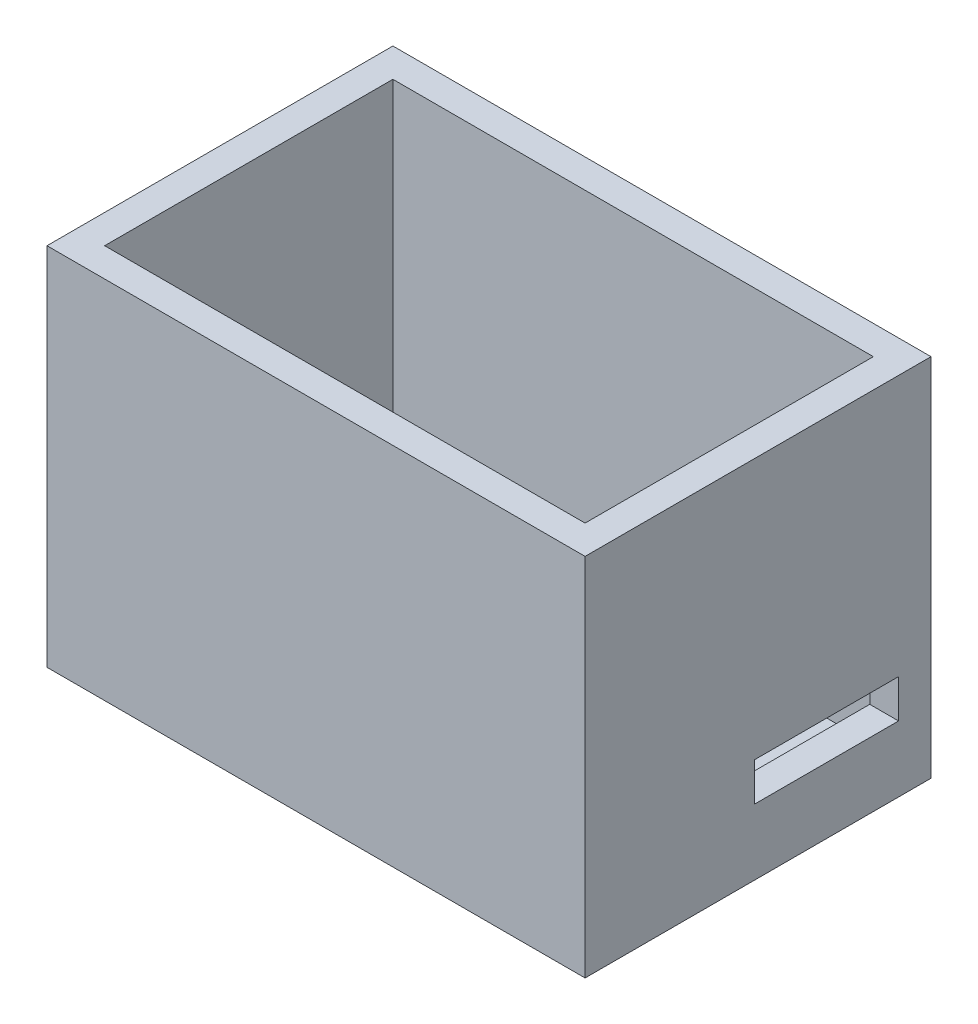
SolidWorks part; units mm, degrees
ref_plane "Plano frontal" through (0, 0, 0) normal (0, 0, 1) x (1, 0, 0)
ref_plane "Plano superior" through (0, 0, 0) normal (0, 1, 0) x (1, 0, 0)
ref_plane "Plano direito" through (0, 0, 0) normal (1, 0, 0) x (0, 0, -1)
sketch "Esboço1" plane through (0, 0, 0) normal (0, 1, 0) x (1, 0, 0)
  line L1 (-60.3352, 26.656) -> (-10.3352, 26.656)
  line L2 (-60.3352, 26.656) -> (-60.3352, -3.344)
  line L3 (-60.3352, -3.344) -> (-10.3352, -3.344)
  line L4 (-10.3352, 26.656) -> (-10.3352, -3.344)
  dimension "D1" = 50
  dimension "D2" = 30
extrude "Ressalto-extrusão1" add sketch "Esboço1" along normal blind 35
shell "Casca1" thickness 3
sketch "Esboço3" plane through (-7.3352, 0, 0) normal (1, 0, 0) x (0, 0, -1)
  line L1 (26.2815, 7.8528) -> (11.2815, 7.8528)
  line L2 (26.2815, 7.8528) -> (26.2815, 3.8528)
  line L3 (26.2815, 3.8528) -> (11.2815, 3.8528)
  line L4 (11.2815, 7.8528) -> (11.2815, 3.8528)
  dimension "D1" = 15
extrude "Corte-extrusão2" cut sketch "Esboço3" against normal blind 35
sketch "Esboço4" plane through (0, 0, 0) normal (0, 1, 0) x (1, 0, 0)
  line L0 (-35.3352, 26.656) -> (-35.3352, -3.344) construction
  line L1 (-10.3352, 26.656) -> (-60.3352, 26.656) construction
  line L2 (-60.3352, -3.344) -> (-10.3352, -3.344) construction
  line L3 (-10.3352, 11.656) -> (-60.3352, 11.656) construction
  line L4 (-10.3352, -3.344) -> (-10.3352, 26.656) construction
  line L5 (-60.3352, 26.656) -> (-60.3352, -3.344) construction
  circle A0 centre (-44.2282, 17.7212) radius 2
  circle A1 centre (-44.2282, 5.5908) radius 2
  circle A2 centre (-26.4422, 5.5908) radius 2
  circle A3 centre (-26.4422, 17.7212) radius 2
extrude "Corte-extrusão3" cut sketch "Esboço4" against normal through all
